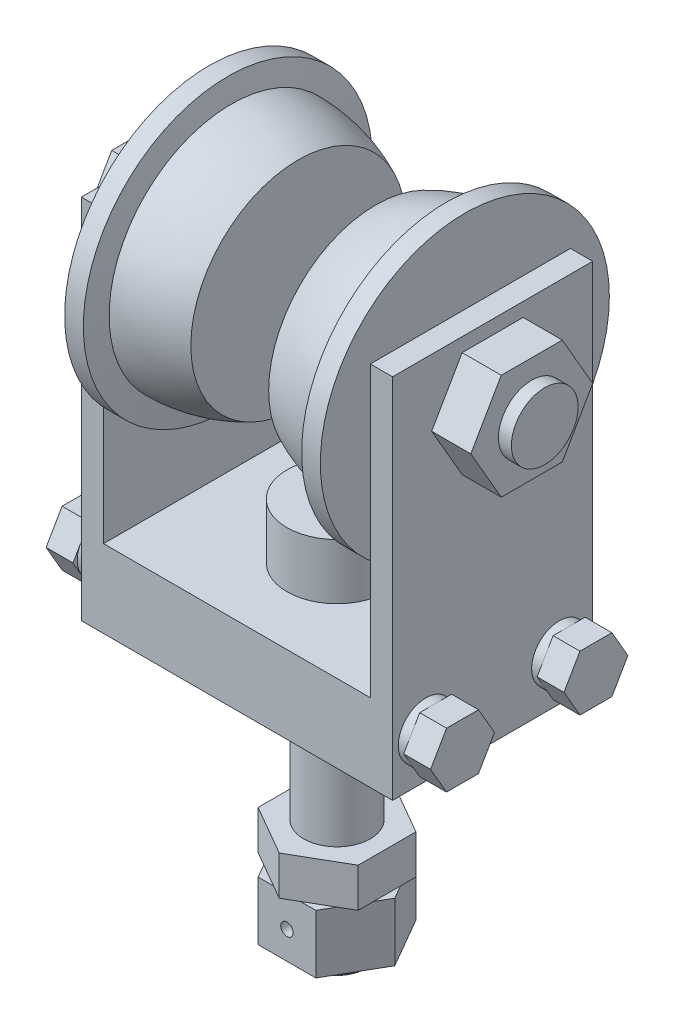
SolidWorks part; units mm, degrees
ref_plane "Front" through (0, 0, 0) normal (0, 0, 1) x (1, 0, 0)
ref_plane "Top" through (0, 0, 0) normal (0, 1, 0) x (1, 0, 0)
ref_plane "Right" through (0, 0, 0) normal (1, 0, 0) x (0, 0, -1)
ref_plane "Z PLANE" through (0, 0, 0) normal (0, 0, 1) x (1, 0, 0)
ref_plane "YOKE BOTTOM" through (0, 0, 0) normal (0, 1, 0) x (-1, 0, 0)
ref_plane "X PLANE" through (0, 0, 0) normal (1, 0, 0) x (0, 0, -1)
sketch "YOKE CROSS SECTION" plane through (0, 0, 0) normal (1, 0, 0) x (0, 0, -1)
  line L0 (0, 0) -> (0, 57.0916) construction
  line L1 (0, 84.8167) -> (0, -84.8167) construction
  line L2 (-57.15, 0) -> (57.15, 0)
  line L3 (69.1602, 0) -> (-69.1602, 0) construction
  line L4 (57.15, 0) -> (57.15, 44.45)
  line L5 (-57.15, 0) -> (-57.15, 44.45)
  line L6 (57.15, 44.45) -> (-57.15, 44.45)
  point P12 (0, 44.45)
  dimension "D1" = 44.45
  dimension "D2" = 114.3
ref_plane "1/2 YOKE LENGTH (A)" through (76.2, 0, 0) normal (1, 0, 0) x (0, 0, -1)
extrude "YOKE" add sketch "YOKE CROSS SECTION" along normal up to surface (76.2 mm away) up to plane "1/2 YOKE LENGTH (A)"
sketch "SIDEPLATE PROFILE" plane through (76.2, 0, 0) normal (1, 0, 0) x (0, 0, -1)
  line L0 (0, 0) -> (0, 74.7424) construction
  line L1 (0, 84.8167) -> (0, -84.8167) construction
  line L2 (-57.15, 0) -> (57.15, 0)
  line L3 (57.15, 0) -> (57.15, 209.55)
  line L4 (-57.15, 0) -> (-57.15, 209.55)
  line L5 (57.15, 209.55) -> (-57.15, 209.55)
  point P11 (0, 209.55)
  dimension "D1" = 209.55
ref_plane "WHEEL HEIGHT" through (0, 171.45, 0) normal (0, 1, 0) x (-1, 0, 0)
ref_plane "SCREW LOCATION X" through (0, 0, 38.1) normal (0, 0, 1) x (1, 0, 0)
ref_plane "SCREW LOCATION Y" through (0, 25.4, 0) normal (0, 1, 0) x (-1, 0, 0)
extrude "SIDEPLATE" add sketch "SIDEPLATE PROFILE" along normal blind 12.7
sketch "WHEEL PIN NUT PROFILE" plane through (88.9, 0, 0) normal (1, 0, 0) x (0, 0, -1)
  line L0 (0, 84.8167) -> (0, -84.8167) construction
  line L1 (34.8287, 171.45) -> (17.4143, 201.6125)
  line L2 (17.4143, 201.6125) -> (-17.4143, 201.6125)
  line L3 (-17.4143, 201.6125) -> (-34.8287, 171.45)
  line L4 (-34.8287, 171.45) -> (-17.4143, 141.2875)
  line L5 (-17.4143, 141.2875) -> (17.4143, 141.2875)
  line L6 (17.4143, 141.2875) -> (34.8287, 171.45)
  line L7 (69.1602, 171.45) -> (-69.1602, 171.45) construction
  circle A0 centre (0, 171.45) radius 30.1625 construction
  dimension "D1" = 60.325
extrude "WHEEL PIN NUT" add sketch "WHEEL PIN NUT PROFILE" along normal blind 22.352
sketch "WHEEL PIN PROJECTION PROFILE" plane through (111.252, 0, 0) normal (1, 0, 0) x (0, 0, -1)
  line L0 (0, 84.8167) -> (0, -84.8167) construction
  line L1 (69.1602, 171.45) -> (-69.1602, 171.45) construction
  circle A0 centre (0, 171.45) radius 19.05
  dimension "D1" = 38.1
extrude "WHEEL PIN PROJECTION" add sketch "WHEEL PIN PROJECTION PROFILE" along normal blind 7.4168
sketch "LOCKNUTS PROFILE" plane through (88.9, 0, 0) normal (1, 0, 0) x (0, 0, -1)
  line L0 (-38.1, 84.8167) -> (-38.1, -84.8167) construction
  line L1 (50, 25.4) -> (-50, 25.4) construction
  circle A0 centre (-38.1, 25.4) radius 15.8115
  dimension "D1" = 31.623
extrude "LOCKNUTS" add sketch "LOCKNUTS PROFILE" along normal blind 5.5626
sketch "SCREWS PROFILE" plane through (94.4626, 0, 0) normal (1, 0, 0) x (0, 0, -1)
  line L0 (50, 25.4) -> (-50, 25.4) construction
  line L1 (-19.8425, 25.4) -> (-28.9712, 41.2115)
  line L2 (-28.9712, 41.2115) -> (-47.2288, 41.2115)
  line L3 (-47.2288, 41.2115) -> (-56.3575, 25.4)
  line L4 (-56.3575, 25.4) -> (-47.2288, 9.5885)
  line L5 (-47.2288, 9.5885) -> (-28.9712, 9.5885)
  line L6 (-28.9712, 9.5885) -> (-19.8425, 25.4)
  line L7 (-38.1, 84.8167) -> (-38.1, -84.8167) construction
  circle A0 centre (-38.1, 25.4) radius 15.8115 construction
  dimension "D1" = 31.623
extrude "SCREWS" add sketch "SCREWS PROFILE" along normal blind 15.3416
sketch "PROFILE" plane through (0, 44.45, 0) normal (0, 1, 0) x (-1, 0, 0)
  line L0 (84.8167, 0) -> (-84.8167, 0) construction
  line L1 (0, 83.2389) -> (0, -83.2389) construction
  circle A0 centre (0, 0) radius 28.575
  dimension "D1" = 57.15
extrude "KING BOLT HEAD" add sketch "PROFILE" along normal blind 31.75
mirror "Mirror1" about plane through (0, 0, 0) normal (0, 0, 1) of "SCREWS", "LOCKNUTS"
mirror "Mirror5" about plane through (0, 0, 0) normal (1, 0, 0) of bodies 112
ref_plane "TOP OF NUT" through (0, -82.55, 0) normal (0, 1, 0) x (-1, 0, 0)
sketch "DIA." plane through (0, 0, 0) normal (0, -1, 0) x (1, 0, 0)
  line L0 (84.8167, 0) -> (-84.8167, 0) construction
  line L1 (0, -83.2389) -> (0, 83.2389) construction
  circle A0 centre (0, 0) radius 19.05
  dimension "D1" = 38.1
extrude "KING BOLT" add sketch "DIA." along normal up to surface (82.55 mm away) up to plane "TOP OF NUT"
sketch "KING BOLT JAN NUT PROFILE" plane through (0, -82.55, 0) normal (0, -1, 0) x (1, 0, 0)
  line L0 (84.8167, 0) -> (-84.8167, 0) construction
  line L1 (0, -32.9956) -> (28.575, -16.4978)
  line L2 (28.575, -16.4978) -> (28.575, 16.4978)
  line L3 (28.575, 16.4978) -> (0, 32.9956)
  line L4 (0, 32.9956) -> (-28.575, 16.4978)
  line L5 (-28.575, 16.4978) -> (-28.575, -16.4978)
  line L6 (-28.575, -16.4978) -> (0, -32.9956)
  line L7 (0, -83.2389) -> (0, 83.2389) construction
  circle A0 centre (0, 0) radius 28.575 construction
  dimension "D1" = 57.15
extrude "KING BOLT JAM NUT" add sketch "KING BOLT JAN NUT PROFILE" along normal blind 22.352
sketch "KING BOLT NUT PROFILE" plane through (0, -104.902, 0) normal (0, -1, 0) x (1, 0, 0)
  line L1 (32.9956, 0) -> (16.4978, 28.575)
  line L2 (16.4978, 28.575) -> (-16.4978, 28.575)
  line L3 (-16.4978, 28.575) -> (-32.9956, 0)
  line L4 (-32.9956, 0) -> (-16.4978, -28.575)
  line L5 (-16.4978, -28.575) -> (16.4978, -28.575)
  line L6 (16.4978, -28.575) -> (32.9956, 0)
  line L10 (0, -83.2389) -> (0, 83.2389) construction
  line L11 (84.8167, 0) -> (-84.8167, 0) construction
  circle A0 centre (0, 0) radius 28.575 construction
  dimension "D1" = 57.15
extrude "KING BOLT NUT" add sketch "KING BOLT NUT PROFILE" along normal blind 33.4518
sketch "Sketch5" plane through (0, -138.3538, 0) normal (0, -1, 0) x (1, 0, 0)
  circle A0 centre (0, 0) radius 19.05 construction
  circle A1 centre (0, 0) radius 19.05
extrude "EXTENDED KING BOLT" add sketch "Sketch5" along normal blind 9.525
chamfer "Chamfer1" distance 2.3812 angle 45 1 edges at (0, -147.8788, -19.05)
ref_plane "MOUNTING REF PLANE" through (0, -34.925, 0) normal (0, 1, 0) x (-1, 0, 0)
sketch "Sketch6" plane through (0, 0, 0) normal (0, 0, 1) x (1, 0, 0)
  line L0 (73.025, 198.4375) -> (73.025, 254)
  line L1 (60.325, 241.3) -> (62.3365, 254)
  line L2 (76.2, 171.45) -> (22.225, 171.45)
  line L3 (22.225, 171.45) -> (22.225, 232.7219)
  line L4 (76.2, 171.45) -> (76.2, 198.4375)
  line L5 (76.2, 198.4375) -> (76.2, 171.45)
  line L6 (76.2, 198.4375) -> (73.025, 198.4375)
  line L7 (62.3365, 254) -> (73.025, 254)
  line L8 (69.1602, 171.45) -> (-69.1602, 171.45) construction
  line L9 (76.2, -75.0522) -> (76.2, 75.0522) construction
  arc A0 (60.325, 241.3) -> (22.225, 232.7219) centre (60.325, 152.4) ccw
  dimension "D9" = 88.9
  dimension "D1" = 3.175
  dimension "D2" = 13.8635
  dimension "D3" = 15.875
  dimension "D4" = 53.975
  dimension "D5" = 26.9875
  dimension "D6" = 82.55
  dimension "D7" = 69.85
  dimension "D8" = 61.2719
revolve "WHEEL" add sketch "Sketch6" angle 360 about L2
mirror "Mirror6" about plane through (0, 0, 0) normal (1, 0, 0) of "WHEEL"
sketch "Sketch7" plane through (0, 0, 28.575) normal (0, 0, 1) x (1, 0, 0)
  line L0 (0, -83.2389) -> (0, 83.2389) construction
  line L1 (-16.4978, -138.3538) -> (-32.9956, -138.3538) construction
  circle A0 centre (0, -122.4788) radius 3.5719
  point P6 (-24.7467, -138.3538)
  dimension "D1" = 7.1437
  dimension "D2" = 15.875
extrude "COTTER PIN HOLE" cut sketch "Sketch7" against normal up to next
sketch "Sketch8" plane through (0, 0, 0) normal (0, -1, 0) x (1, 0, 0)
  circle A0 centre (0, 0) radius 25.4
  circle A1 centre (0, 0) radius 30.1625
  dimension "D1" = 60.325
  dimension "D2" = 50.8
extrude "SPACER" add sketch "Sketch8" along normal blind 12.7
ref_plane "TREAD OF TRACK" through (0, 101.6, 0) normal (0, 1, 0) x (-1, 0, 0)
